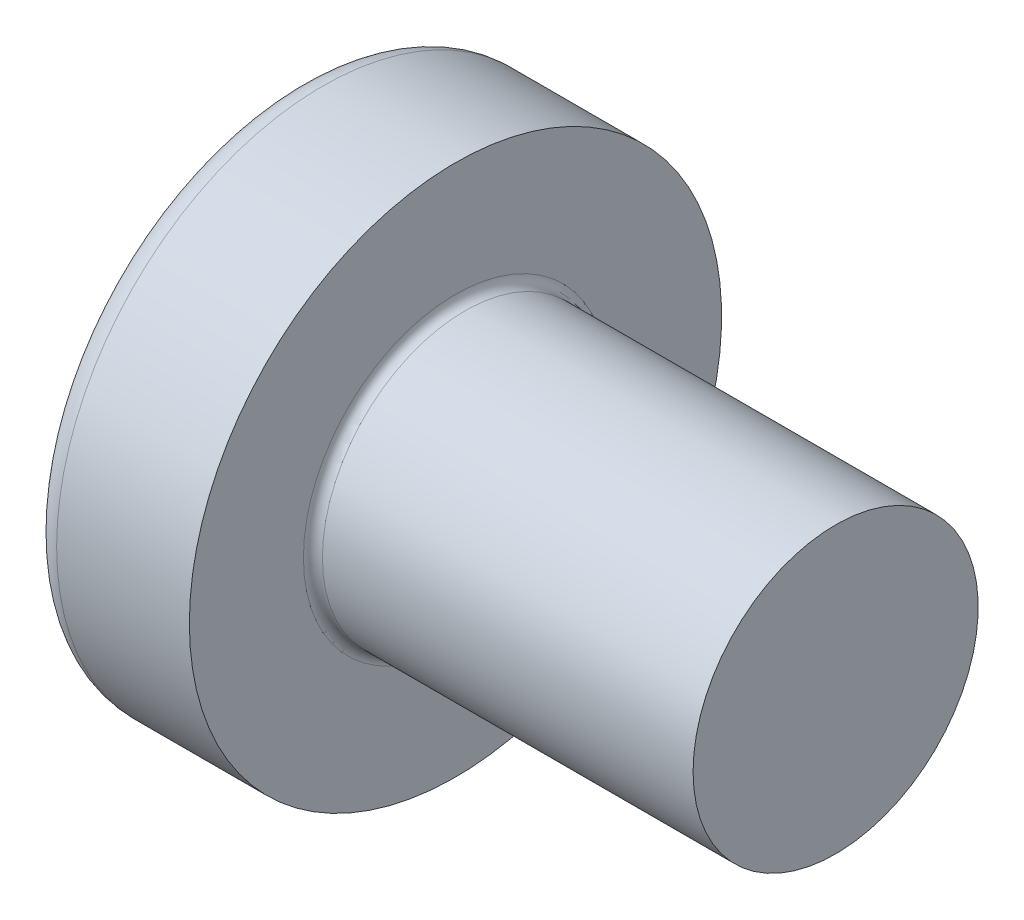
SolidWorks part; units mm, degrees
ref_plane "Plane1" through (0, 0, 0) normal (0, 0, 1) x (1, 0, 0)
ref_plane "Plane2" through (0, 0, 0) normal (0, 1, 0) x (1, 0, 0)
ref_plane "Plane3" through (0, 0, 0) normal (1, 0, 0) x (0, 0, -1)
revolve "Base-Revolve" add sketch "BodySke"
sketch "BodySke" plane through (0, 0, 0) normal (0, 0, 1) x (1, 0, 0)
  line L0 (2.4, 1.5) -> (2.4, 2.8)
  line L1 (2.65, 6.35) -> (2.65, -3.175) construction
  line L2 (-25.4, 0) -> (127, 0) construction
  line L3 (6.4, 0) -> (0, 0)
  line L4 (2.4, 1.5) -> (6.4, 1.5)
  line L5 (6.4, 1.5) -> (6.4, 0)
  line L6 (1.0035, 2.8) -> (2.4, 2.8)
  line L8 (2.4, 6.35) -> (2.4, -3.175) construction
  arc A0 (0.7754, 2.6744) -> (0, 0) centre (5, 0) ccw
  arc A2 (0.7754, 2.6744) -> (1.0035, 2.8) centre (1.0035, 2.53) cw
  dimension "Head_fillet_rad" = 0.27
  dimension "Head_crown_rad" = 5
  dimension "Head_ht" = 2.4
  dimension "Diameter" = 3
  dimension "Length" = 4
  dimension "Head_dia" = 5.6
  dimension "Advance" = 0.5
  dimension "Thread_nom" = 4
cosmetic thread "ThreadCosmetic" [suppressed]
fillet "Fillet1" radius 0.1 1 edges at (2.4, 0, 1.5)
sketch "Sketch3" plane through (0, 0, 0) normal (1, 0, 0) x (0, 0, -1)
  line L0 (0.37, -1.4) -> (-0.37, -1.4)
  line L1 (0.37, -1.4) -> (0.37, 1.4)
  line L2 (-0.37, 1.4) -> (0.37, 1.4)
  line L3 (-0.37, 1.4) -> (-0.37, -1.4)
  dimension "D1" = 1.4
  dimension "Cross_dia" = 2.8
  dimension "D2" = 0.37
  dimension "Cross_width" = 0.74
ref_plane "Plane4" through (1.75, 0, 0) normal (1, 0, 0) x (0, 0, -1)
sketch "Sketch4" plane through (1.75, 0, 0) normal (1, 0, 0) x (0, 0, -1)
  line L0 (0.37, -0.5275) -> (-0.37, -0.5275)
  line L1 (0.37, -0.5275) -> (0.37, 0.5275)
  line L2 (-0.37, 0.5275) -> (0.37, 0.5275)
  line L3 (-0.37, 0.5275) -> (-0.37, -0.5275)
  dimension "D1" = 0.74
  dimension "D2" = 1.055
  dimension "D3" = 0.37
  dimension "D4" = 0.5275
loft "Recess" cut profiles "Sketch3", "Sketch4"
pattern_circular "RecPat" count 2 every 90 about axis through (0, 0, 0) along (1, 0, 0) of "Recess"
sketch "RecCorSke" plane through (0, 0, 0) normal (0, 0, 1) x (1, 0, 0)
  line L0 (-3.175, 0) -> (15.875, 0) construction
  line L1 (-25.4, 0) -> (127, 0) construction
  line L2 (0, 0) -> (0, 0.6784)
  line L3 (0, 0.6784) -> (1.75, 0.556)
  line L4 (1.75, 0.556) -> (1.9307, 0)
  line L5 (1.9307, 0) -> (0, 0)
  dimension "Diameter" = 1.112
  dimension "Depth" = 1.75
  dimension "Draft_angle" = 4
  dimension "Bottom_angle" = 18
revolve "RecessCore" cut sketch "RecCorSke" angle 360 about L0
sketch "ThdSchSke" plane through (0, 0, 0) normal (0, 0, 1) x (1, 0, 0)
  line L0 (3.4, -1.2195) -> (3.2036, -1.5)
  line L1 (3.4, -1.2195) -> (3.5964, -1.5)
  line L2 (3.5964, -1.5) -> (3.5964, -1.875)
  line L3 (-3.175, 0) -> (5.1513, 0) construction
  line L5 (3.5964, -1.875) -> (3.2036, -1.875)
  line L6 (3.2036, -1.875) -> (3.2036, -1.5)
  dimension "Thread_minor" = 2.439
  dimension "Diameter" = 3
  dimension "Start" = 3.4
  dimension "SideAngle" = 55
  dimension "VeeAngle" = 70
  dimension "Overcut" = 3.75
revolve "ThreadSchematic" [suppressed] cut sketch "ThdSchSke" angle 360 about L3
pattern_linear "ThdSchPat" [suppressed]
equation "\"D1@Sketch3\" = \"Cross_dia@Sketch3\" / 2"
equation "\"D2@Sketch3\" = \"Cross_width@Sketch3\" / 2"
equation "\"Depth@RecCorSke\" = \"Cross_depth@Plane4\""
equation "\"D1@Sketch4\" = \"Cross_width@Sketch3\""
equation "\"D2@Sketch4\" = \"Cross_dia@Sketch3\" - 2.0 * \"Cross_depth@Plane4\" * tan(26.5  * 0.017453292)"
equation "\"D3@Sketch4\" = \"D1@Sketch4\" / 2"
equation "\"D4@Sketch4\" = \"D2@Sketch4\" / 2"
equation "\"Thread_length@ThreadCosmetic\" = ((sgn( (\"Length@BodySke\" - \"Advance@BodySke\" * 2.0 ) - \"Thread_nom@BodySke\" )-1)*( (\"Length@BodySke\" - \"Advance@BodySke\" * 2.0 ) - \"Thread_nom@BodySke\" ))/-2+ \"Thread_nom@BodySke\""
equation "\"Thread_minor@ThdSchSke\" = \"Thread_minor@ThreadCosmetic\""
equation "\"Diameter@ThdSchSke\" = \"Diameter@BodySke\""
equation "\"Overcut@ThdSchSke\" = \"Diameter@BodySke\" * 1.25"
equation "\"Start@ThdSchSke\" = \"Head_ht@BodySke\" + \"Length@BodySke\" - \"Thread_length@ThreadCosmetic\"  '---Non-countersunk---"
equation "\"Num_threads@ThdSchPat\" = int( \"Thread_length@ThreadCosmetic\" / \"Advance@BodySke\" + 0.999 )  + 1"
equation "\"Advance@ThdSchPat\" = \"Thread_length@ThreadCosmetic\" /  (\"Num_threads@ThdSchPat\" - 1) 'relax it"
